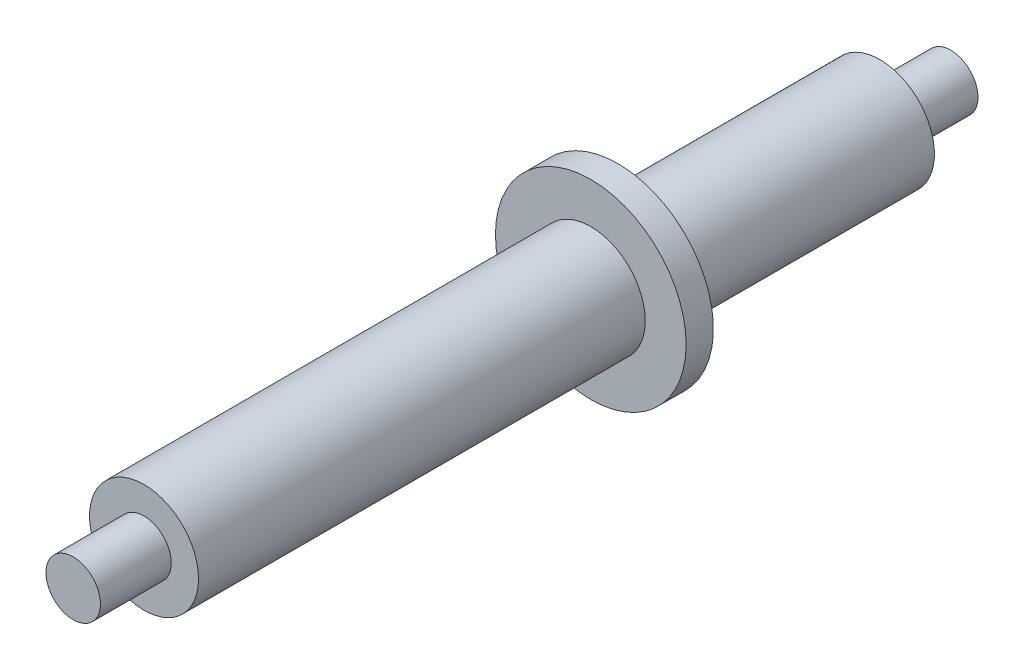
SolidWorks part; units mm, degrees
material "Сталь ШХ15 ГОСТ 801-78"
ref_plane "Plane1" through (0, 0, 0) normal (0, 0, 1) x (1, 0, 0)
ref_plane "Plane2" through (0, 0, 0) normal (0, 1, 0) x (1, 0, 0)
ref_plane "Plane3" through (0, 0, 0) normal (1, 0, 0) x (0, 0, -1)
sketch "Эскиз1" plane through (0, 0, 0) normal (0, 0, 1) x (1, 0, 0)
  circle A0 centre (0, 0) radius 2
  dimension "D1" = 4
extrude "Бобышка-Вытянуть1" add sketch "Эскиз1" against normal up to surface (27.0135 mm away) from surface contours A0
sketch "Эскиз2" plane through (0, 0, 30.4) normal (0, 0, 1) x (1, 0, 0)
  circle A0 centre (0, 0) radius 1
  dimension "D1" = 2
extrude "Бобышка-Вытянуть2" add sketch "Эскиз2" along normal up to surface (2.6 mm away) contours A0
sketch "Эскиз4" plane through (0, 0, 3.3865) normal (0, 0, -1) x (-1, 0, 0)
  circle A0 centre (0, 0) radius 1
  dimension "D1" = 2
extrude "Бобышка-Вытянуть3" add sketch "Эскиз4" along normal up to surface (2.6 mm away)
sketch "Эскиз6" plane through (0, 0, 3.3865) normal (0, 0, -1) x (-1, 0, 0)
  circle A0 centre (0, 0) radius 3.5
  dimension "D1" = 7
extrude "Бобышка-Вытянуть5" add sketch "Эскиз6" along normal up to surface (1 mm away) from surface
